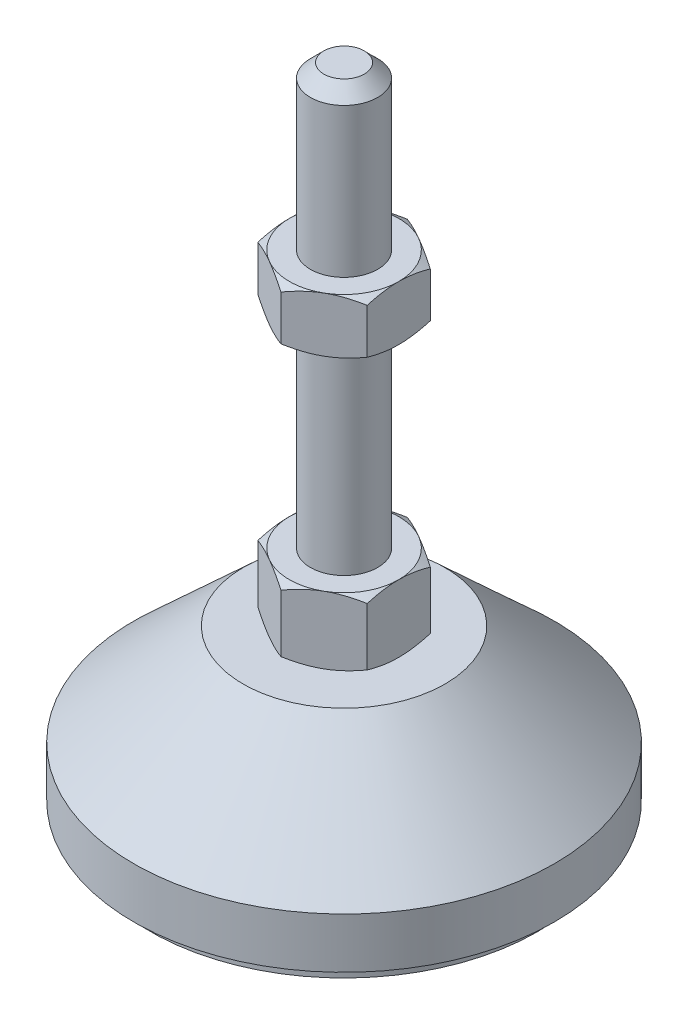
SolidWorks part; units mm, degrees
ref_plane "Спереди" through (0, 0, 0) normal (0, 0, 1) x (1, 0, 0)
ref_plane "Сверху" through (0, 0, 0) normal (0, 1, 0) x (1, 0, 0)
ref_plane "Справа" through (0, 0, 0) normal (1, 0, 0) x (0, 0, -1)
sketch "Эскиз1" plane through (0, 0, 0) normal (0, 0, 1) x (1, 0, 0)
  line L0 (0, 0) -> (-23, 0)
  line L1 (-23, 0) -> (-23, 2)
  line L2 (-23, 2) -> (-25, 2)
  line L3 (-25, 2) -> (-25, 8)
  line L4 (-25, 8) -> (-12, 20)
  line L5 (-12, 20) -> (-4, 20)
  line L12 (-4, 28) -> (-4, 76.4)
  line L13 (-4, 76.4) -> (-2.4, 78)
  line L14 (-2.4, 78) -> (0, 78)
  line L15 (0, 78) -> (0, 0) construction
  line L16 (-4, 20) -> (0, 20) construction
  line L17 (0, 0) -> (0, 78)
  line L18 (0, 0) -> (0, -7.9595) construction
  line L19 (-4, 28) -> (-4, 20)
  point P8 (-4, 52.2)
  point P23 (-8, 20)
  dimension "D1" = 8
  dimension "D2" = 20
  dimension "D3" = 8
  dimension "D4" = 50
  dimension "D5" = 4
  dimension "D6" = 1.6
  dimension "D7" = 45
  dimension "D8" = 24
  dimension "D9" = 2
  dimension "D10" = 50
  dimension "D11" = 6
revolve "Повернуть1" add sketch "Эскиз1" angle 360 about L17
sketch "Эскиз2" plane through (0, 20, 0) normal (0, 1, 0) x (1, 0, 0)
  line L1 (0, 7.5056) -> (-6.5, 3.7528)
  line L2 (-6.5, 3.7528) -> (-6.5, -3.7528)
  line L3 (-6.5, -3.7528) -> (0, -7.5056)
  line L4 (0, -7.5056) -> (6.5, -3.7528)
  line L5 (6.5, -3.7528) -> (6.5, 3.7528)
  line L6 (6.5, 3.7528) -> (0, 7.5056)
  circle A0 centre (0, 0) radius 6.5 construction
  dimension "D1" = 13
extrude "Бобышка-Вытянуть1" add sketch "Эскиз2" along normal up to vertex (8 mm away) up to point (-4, 28, 0)
ref_plane "Плоскость1" through (0, 52.2, 0) normal (0, 1, 0) x (1, 0, 0)
sketch "Эскиз3" plane through (0, 52.2, 0) normal (0, 1, 0) x (1, 0, 0)
  line L6 (6.5, 3.7528) -> (0, 7.5056)
  line L7 (0, 7.5056) -> (-6.5, 3.7528)
  line L8 (-6.5, 3.7528) -> (-6.5, -3.7528)
  line L9 (-6.5, -3.7528) -> (0, -7.5056)
  line L10 (0, -7.5056) -> (6.5, -3.7528)
  line L11 (6.5, -3.7528) -> (6.5, 3.7528)
  line L12 (6.5, 3.7528) -> (0, 7.5056)
  line L13 (0, 7.5056) -> (-6.5, 3.7528)
  line L14 (-6.5, 3.7528) -> (-6.5, -3.7528)
  line L15 (-6.5, -3.7528) -> (0, -7.5056)
  line L16 (0, -7.5056) -> (6.5, -3.7528)
  line L17 (6.5, -3.7528) -> (6.5, 3.7528)
  dimension "D1" = 0
extrude "Бобышка-Вытянуть2" add sketch "Эскиз3" along normal blind 6.5
sketch "Эскиз4" plane through (0, 0, 0) normal (0, 0, 1) x (1, 0, 0)
  line L0 (-6.5, 58.7) -> (-12.1292, 55.45)
  line L1 (-12.1292, 55.45) -> (-12.1292, 58.7)
  line L2 (-12.1292, 58.7) -> (-6.5, 58.7)
  line L3 (-12.1292, 55.45) -> (-6.5, 52.2)
  line L4 (50, 52.2) -> (-50, 52.2) construction
  line L5 (-6.5, 52.2) -> (-12.1292, 52.2)
  line L6 (-12.1292, 52.2) -> (-12.1292, 55.45)
  line L7 (-6.5, 58.7) -> (-6.5, 52.2) construction
  line L8 (-6.5, 28) -> (-13.4282, 28)
  line L9 (-13.4282, 28) -> (-13.4282, 24)
  line L10 (-13.4282, 24) -> (-6.5, 28)
  line L11 (-6.5, 20) -> (-13.4282, 24)
  line L12 (-13.4282, 24) -> (-13.4282, 20)
  line L13 (-13.4282, 20) -> (-6.5, 20)
  line L14 (0, 78) -> (0, 96.3793) construction
  dimension "D1" = 30
  dimension "D2" = 30
revolve "Вырез-Повернуть2" cut sketch "Эскиз4" angle 360 about L14
